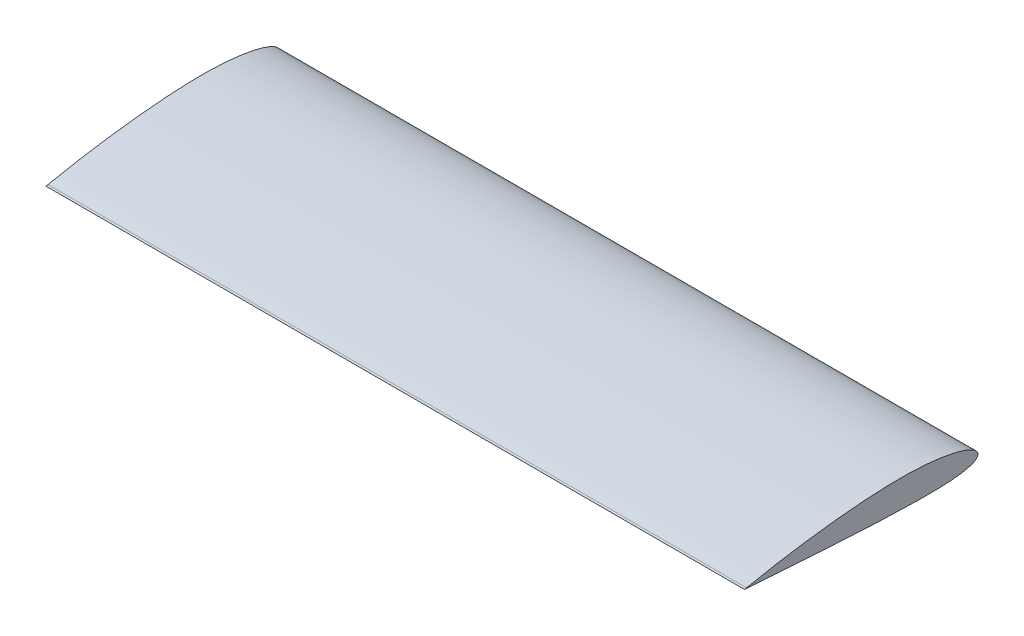
SolidWorks part; units mm, degrees
ref_plane "Front Plane" through (0, 0, 0) normal (0, 0, 1) x (1, 0, 0)
ref_plane "Top Plane" through (0, 0, 0) normal (0, 1, 0) x (1, 0, 0)
ref_plane "Right Plane" through (0, 0, 0) normal (1, 0, 0) x (0, 0, -1)
curve "Curve1"
  spline degree 3 poles (0, 0.3331, 265.0223) (0, 0.3612, 264.8874) (0, 0.4734, 264.3486) (0, 0.7244, 263.1394) (0, 1.1375, 261.1317) (0, 1.7046, 258.3372) (0, 2.4163, 254.7721) (0, 3.2593, 250.4573) (0, 4.2191, 245.4178) (0, 5.2801, 239.6836) (0, 6.4242, 233.2882) (0, 7.6336, 226.27) (0, 8.8901, 218.6706) (0, 10.1742, 210.5358) (0, 11.4671, 201.9146) (0, 12.7502, 192.8593) (0, 14.0042, 183.4251) (0, 15.2107, 173.6696) (0, 16.3524, 163.6528) (0, 17.4092, 153.4362) (0, 18.3659, 143.0834) (0, 19.2031, 132.6586) (0, 19.9071, 122.227) (0, 20.4613, 111.8422) (0, 20.8584, 101.5539) (0, 21.0255, 91.4257) (0, 20.9612, 81.536) (0, 20.6641, 71.9656) (0, 20.1376, 62.7774) (0, 19.3898, 54.0325) (0, 18.4336, 45.788) (0, 17.2852, 38.098) (0, 15.9649, 31.0117) (0, 14.495, 24.5739) (0, 12.902, 18.8236) (0, 11.2104, 13.7947) (0, 9.4471, 9.5138) (0, 7.6355, 6.0009) (0, 5.7937, 3.2647) (0, 3.9255, 1.3069) (0, 1.9937, 0.1287) (0, -0.0151, -0.1511) (0, -1.9271, 0.52) (0, -3.5893, 2.0452) (0, -5.0447, 4.3081) (0, -6.3407, 7.308) (0, -7.4838, 11.04) (0, -8.4754, 15.4883) (0, -9.3129, 20.6286) (0, -9.9955, 26.4308) (0, -10.5244, 32.86) (0, -10.904, 39.8778) (0, -11.1403, 47.4429) (0, -11.2433, 55.5113) (0, -11.2241, 64.0365) (0, -11.0979, 72.9697) (0, -10.8802, 82.26) (0, -10.5897, 91.8545) (0, -10.2419, 101.7137) (0, -9.861, 111.7928) (0, -9.4003, 122.0296) (0, -8.883, 132.3475) (0, -8.3203, 142.6718) (0, -7.7281, 152.94) (0, -7.1174, 163.0894) (0, -6.4999, 173.0577) (0, -5.8836, 182.7834) (0, -5.2772, 192.2065) (0, -4.6871, 201.2683) (0, -4.1184, 209.9123) (0, -3.5763, 218.0842) (0, -3.0636, 225.7326) (0, -2.5856, 232.8091) (0, -2.1445, 239.2687) (0, -1.7446, 245.0702) (0, -1.3887, 250.1764) (0, -1.0804, 254.5544) (0, -0.8233, 258.176) (0, -0.6195, 261.0175) (0, -0.4724, 263.0606) (0, -0.383, 264.2917) (0, -0.3431, 264.8404) (0, -0.3331, 264.9777) knots 0 0 0 0 0.000764 0.003052 0.00685 0.012132 0.018868 0.027013 0.036517 0.047321 0.059357 0.072551 0.08682 0.102077 0.118228 0.135171 0.152802 0.171013 0.18969 0.208718 0.227979 0.247354 0.266723 0.285966 0.305032 0.323824 0.342144 0.35988 0.376926 0.393182 0.408553 0.422951 0.436298 0.448523 0.459565 0.469379 0.477934 0.48522 0.491268 0.496168 0.500133 0.503587 0.507041 0.511 0.515876 0.521872 0.529071 0.537495 0.547131 0.557945 0.56989 0.582904 0.596922 0.611866 0.627656 0.644204 0.661417 0.679197 0.697443 0.716134 0.735139 0.754278 0.773432 0.792487 0.811323 0.829826 0.84788 0.865374 0.882198 0.898247 0.913421 0.927622 0.940763 0.952759 0.963533 0.973016 0.981148 0.987875 0.993154 0.996949 0.999236 1 1 1 1
sketch "Sketch1" plane through (0, 0, 0) normal (1, 0, 0) x (0, 0, -1)
  line L0 (0, 0) -> (-267.3818, 0) construction
  line L1 (-265.0223, 0.3331) -> (-267.3818, -0.1584)
  line L2 (-264.9777, -0.3331) -> (-267.3818, -0.1584)
  spline S0 degree 3 poles (-844.5702, 1911.5323) (-379.9343, -28.3306) (-322.3525, -11.5657) (-263.1394, 0.7244) (-261.1317, 1.1375) (-258.3372, 1.7046) (-254.7721, 2.4163) (-250.4573, 3.2593) (-245.4178, 4.2191) (-239.6836, 5.2801) (-233.2882, 6.4242) (-226.27, 7.6336) (-218.6706, 8.8901) (-210.5358, 10.1742) (-201.9146, 11.4671) (-192.8593, 12.7502) (-183.4251, 14.0042) (-173.6696, 15.2107) (-163.6528, 16.3524) (-153.4362, 17.4092) (-143.0834, 18.3659) (-132.6586, 19.2031) (-122.227, 19.9071) (-111.8422, 20.4613) (-101.5539, 20.8584) (-91.4257, 21.0255) (-81.536, 20.9612) (-71.9656, 20.6641) (-62.7774, 20.1376) (-54.0325, 19.3898) (-45.788, 18.4336) (-38.098, 17.2852) (-31.0117, 15.9649) (-24.5739, 14.495) (-18.8236, 12.902) (-13.7947, 11.2104) (-9.5138, 9.4471) (-6.0009, 7.6355) (-3.2647, 5.7937) (-1.3069, 3.9255) (-0.1287, 1.9937) (0.1511, -0.0151) (-0.52, -1.9271) (-2.0452, -3.5893) (-4.3081, -5.0447) (-7.308, -6.3407) (-11.04, -7.4838) (-15.4883, -8.4754) (-20.6286, -9.3129) (-26.4308, -9.9955) (-32.86, -10.5244) (-39.8778, -10.904) (-47.4429, -11.1403) (-55.5113, -11.2433) (-64.0365, -11.2241) (-72.9697, -11.0979) (-82.26, -10.8802) (-91.8545, -10.5897) (-101.7137, -10.2419) (-111.7928, -9.861) (-122.0296, -9.4003) (-132.3475, -8.883) (-142.6718, -8.3203) (-152.94, -7.7281) (-163.0894, -7.1174) (-173.0577, -6.4999) (-182.7834, -5.8836) (-192.2065, -5.2772) (-201.2683, -4.6871) (-209.9123, -4.1184) (-218.0842, -3.5763) (-225.7326, -3.0636) (-232.8091, -2.5856) (-239.2687, -2.1445) (-245.0702, -1.7446) (-250.1764, -1.3887) (-254.5544, -1.0804) (-258.176, -0.8233) (-261.0175, -0.6195) (-263.0606, -0.4724) (-446.8905, 12.8902) (-630.1397, 24.7727) (-678.2662, 1929.8767) knots -0.328567 -0.328567 -0.328567 -0.328567 0.000764 0.003052 0.00685 0.012132 0.018868 0.027013 0.036517 0.047321 0.059357 0.072551 0.08682 0.102077 0.118228 0.135171 0.152802 0.171013 0.18969 0.208718 0.227979 0.247354 0.266723 0.285966 0.305032 0.323824 0.342144 0.35988 0.376926 0.393182 0.408553 0.422951 0.436298 0.448523 0.459565 0.469379 0.477934 0.48522 0.491268 0.496168 0.500133 0.503587 0.507041 0.511 0.515876 0.521872 0.529071 0.537495 0.547131 0.557945 0.56989 0.582904 0.596922 0.611866 0.627656 0.644204 0.661417 0.679197 0.697443 0.716134 0.735139 0.754278 0.773432 0.792487 0.811323 0.829826 0.84788 0.865374 0.882198 0.898247 0.913421 0.927622 0.940763 0.952759 0.963533 0.973016 0.981148 0.987875 0.993154 0.996949 0.999236 2.015432 2.015432 2.015432 2.015432 only from (-265.0223, 0.3331) to (-264.9777, -0.3331) construction
  spline S1 degree 3 poles (-265.0223, 0.3331) (-264.8874, 0.3612) (-264.3486, 0.4734) (-263.1394, 0.7244) (-261.1317, 1.1375) (-258.3372, 1.7046) (-254.7721, 2.4163) (-250.4573, 3.2593) (-245.4178, 4.2191) (-239.6836, 5.2801) (-233.2882, 6.4242) (-226.27, 7.6336) (-218.6706, 8.8901) (-210.5358, 10.1742) (-201.9146, 11.4671) (-192.8593, 12.7502) (-183.4251, 14.0042) (-173.6696, 15.2107) (-163.6528, 16.3524) (-153.4362, 17.4092) (-143.0834, 18.3659) (-132.6586, 19.2031) (-122.227, 19.9071) (-111.8422, 20.4613) (-101.5539, 20.8584) (-91.4257, 21.0255) (-81.536, 20.9612) (-71.9656, 20.6641) (-62.7774, 20.1376) (-54.0325, 19.3898) (-45.788, 18.4336) (-38.098, 17.2852) (-31.0117, 15.9649) (-24.5739, 14.495) (-18.8236, 12.902) (-13.7947, 11.2104) (-9.5138, 9.4471) (-6.0009, 7.6355) (-3.2647, 5.7937) (-1.3069, 3.9255) (-0.1287, 1.9937) (0.1511, -0.0151) (-0.52, -1.9271) (-2.0452, -3.5893) (-4.3081, -5.0447) (-7.308, -6.3407) (-11.04, -7.4838) (-15.4883, -8.4754) (-20.6286, -9.3129) (-26.4308, -9.9955) (-32.86, -10.5244) (-39.8778, -10.904) (-47.4429, -11.1403) (-55.5113, -11.2433) (-64.0365, -11.2241) (-72.9697, -11.0979) (-82.26, -10.8802) (-91.8545, -10.5897) (-101.7137, -10.2419) (-111.7928, -9.861) (-122.0296, -9.4003) (-132.3475, -8.883) (-142.6718, -8.3203) (-152.94, -7.7281) (-163.0894, -7.1174) (-173.0577, -6.4999) (-182.7834, -5.8836) (-192.2065, -5.2772) (-201.2683, -4.6871) (-209.9123, -4.1184) (-218.0842, -3.5763) (-225.7326, -3.0636) (-232.8091, -2.5856) (-239.2687, -2.1445) (-245.0702, -1.7446) (-250.1764, -1.3887) (-254.5544, -1.0804) (-258.176, -0.8233) (-261.0175, -0.6195) (-263.0606, -0.4724) (-264.2917, -0.383) (-264.8404, -0.3431) (-264.9777, -0.3331) knots 0 0 0 0 0.000764 0.003052 0.00685 0.012132 0.018868 0.027013 0.036517 0.047321 0.059357 0.072551 0.08682 0.102077 0.118228 0.135171 0.152802 0.171013 0.18969 0.208718 0.227979 0.247354 0.266723 0.285966 0.305032 0.323824 0.342144 0.35988 0.376926 0.393182 0.408553 0.422951 0.436298 0.448523 0.459565 0.469379 0.477934 0.48522 0.491268 0.496168 0.500133 0.503587 0.507041 0.511 0.515876 0.521872 0.529071 0.537495 0.547131 0.557945 0.56989 0.582904 0.596922 0.611866 0.627656 0.644204 0.661417 0.679197 0.697443 0.716134 0.735139 0.754278 0.773432 0.792487 0.811323 0.829826 0.84788 0.865374 0.882198 0.898247 0.913421 0.927622 0.940763 0.952759 0.963533 0.973016 0.981148 0.987875 0.993154 0.996949 0.999236 1 1 1 1
  point P5 (0, 0)
extrude "Boss-Extrude1" add sketch "Sketch1" along normal mid plane 800
